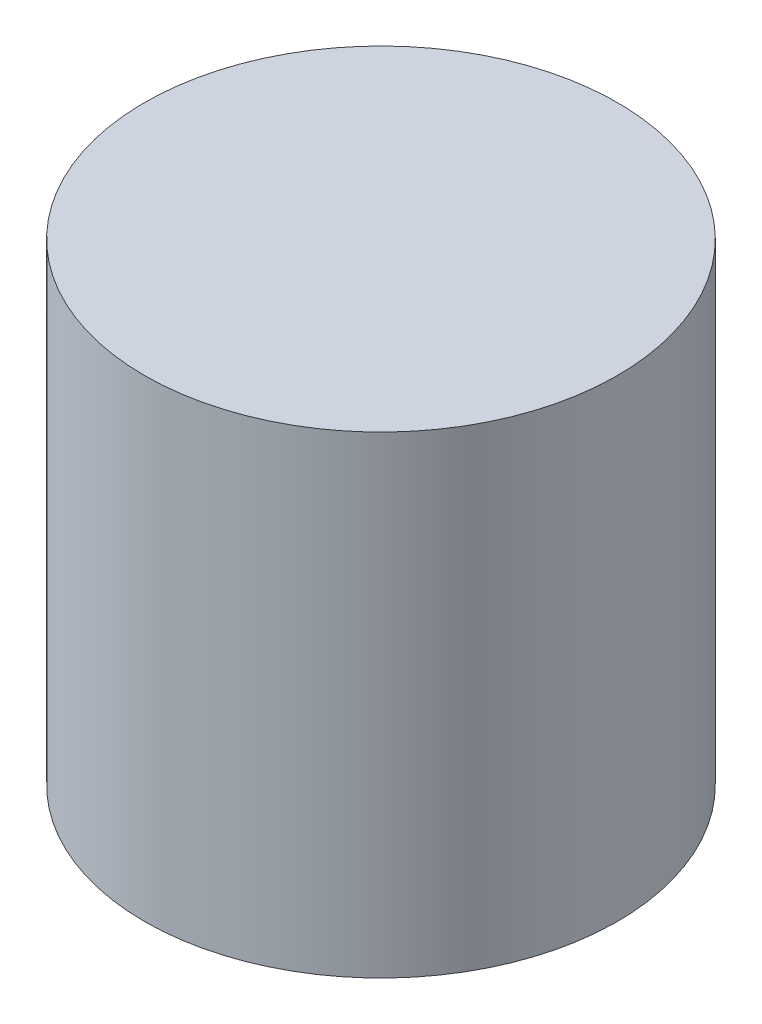
SolidWorks part; units mm, degrees
ref_plane "Front Plane" through (0, 0, 0) normal (0, 0, 1) x (1, 0, 0)
ref_plane "Top Plane" through (0, 0, 0) normal (0, 1, 0) x (1, 0, 0)
ref_plane "Right Plane" through (0, 0, 0) normal (1, 0, 0) x (0, 0, -1)
sketch "Sketch1" plane through (0, 0, 0) normal (0, 1, 0) x (1, 0, 0)
  circle A0 centre (0, 0) radius 12.7
  dimension "D1" = 25.4
extrude "Boss-Extrude1" add sketch "Sketch1" along normal blind 25.4
